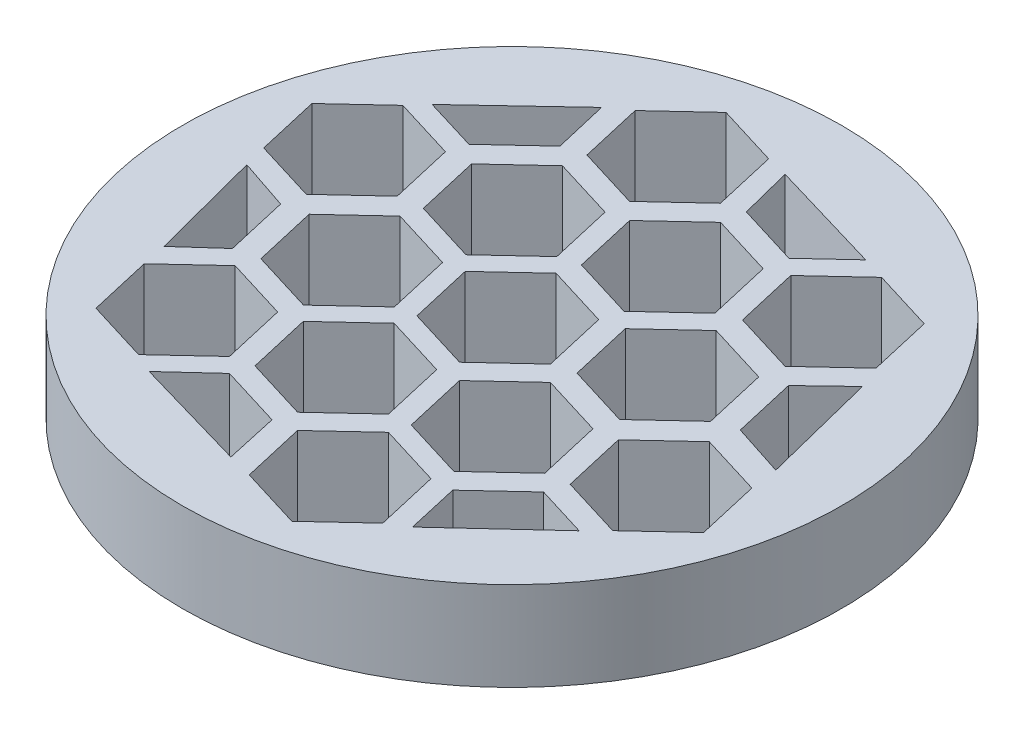
SolidWorks part; units mm, degrees
ref_plane "Ebene vorne" through (0, 0, 0) normal (0, 0, 1) x (1, 0, 0)
ref_plane "Ebene oben" through (0, 0, 0) normal (0, 1, 0) x (1, 0, 0)
ref_plane "Ebene rechts" through (0, 0, 0) normal (1, 0, 0) x (0, 0, -1)
sketch "Skizze1" plane through (0, 0, 0) normal (0, 1, 0) x (1, 0, 0)
  line L0 (3.1154, 1.2037) -> (3.4388, 2.6104)
  line L1 (1.0565, -0.9834) -> (1.3799, 0.4233)
  line L2 (1.3799, 0.4233) -> (0.3234, 1.4067)
  line L3 (0.3234, 1.4067) -> (-1.0565, 0.9834)
  line L4 (-1.0565, 0.9834) -> (-1.3799, -0.4233)
  line L5 (-1.3799, -0.4233) -> (-0.3234, -1.4067)
  line L6 (-0.3234, -1.4067) -> (1.0565, -0.9834)
  line L7 (3.4388, 2.6104) -> (2.3823, 3.5938)
  line L8 (2.3823, 3.5938) -> (1.0024, 3.1705)
  line L9 (1.0024, 3.1705) -> (0.679, 1.7638)
  line L10 (0.679, 1.7638) -> (1.7355, 0.7804)
  line L11 (1.7355, 0.7804) -> (3.1154, 1.2037)
  line L12 (3.9678, -1.6662) -> (4.2912, -0.2595)
  line L13 (4.2912, -0.2595) -> (3.2347, 0.7239)
  line L14 (3.2347, 0.7239) -> (1.8548, 0.3007)
  line L15 (1.8548, 0.3007) -> (1.5314, -1.106)
  line L16 (1.5314, -1.106) -> (2.5879, -2.0894)
  line L17 (2.5879, -2.0894) -> (3.9678, -1.6662)
  line L18 (1.9136, -3.8196) -> (2.237, -2.413)
  line L19 (2.237, -2.413) -> (1.1804, -1.4296)
  line L20 (1.1804, -1.4296) -> (-0.1995, -1.8528)
  line L21 (-0.1995, -1.8528) -> (-0.5229, -3.2595)
  line L22 (-0.5229, -3.2595) -> (0.5337, -4.2429)
  line L23 (0.5337, -4.2429) -> (1.9136, -3.8196)
  line L24 (-0.9621, -3.1449) -> (-0.6387, -1.7382)
  line L25 (-0.6387, -1.7382) -> (-1.6952, -0.7548)
  line L26 (-1.6952, -0.7548) -> (-3.0751, -1.1781)
  line L27 (-3.0751, -1.1781) -> (-3.3985, -2.5847)
  line L28 (-3.3985, -2.5847) -> (-2.342, -3.5682)
  line L29 (-2.342, -3.5682) -> (-0.9621, -3.1449)
  line L30 (-1.8069, -0.3421) -> (-1.4835, 1.0646)
  line L31 (-1.4835, 1.0646) -> (-2.54, 2.048)
  line L32 (-2.54, 2.048) -> (-3.9199, 1.6247)
  line L33 (-3.9199, 1.6247) -> (-4.2433, 0.218)
  line L34 (-4.2433, 0.218) -> (-3.1868, -0.7654)
  line L35 (-3.1868, -0.7654) -> (-1.8069, -0.3421)
  line L36 (0.2105, 1.8075) -> (0.5339, 3.2142)
  line L37 (0.5339, 3.2142) -> (-0.5227, 4.1976)
  line L38 (-0.5227, 4.1976) -> (-1.9026, 3.7743)
  line L39 (-1.9026, 3.7743) -> (-2.226, 2.3676)
  line L40 (-2.226, 2.3676) -> (-1.1694, 1.3842)
  line L41 (-1.1694, 1.3842) -> (0.2105, 1.8075)
  line L42 (6.052, 0.5724) -> (6.3754, 1.9791)
  line L43 (6.3754, 1.9791) -> (5.3189, 2.9625)
  line L44 (5.3189, 2.9625) -> (3.9389, 2.5392)
  line L45 (3.9389, 2.5392) -> (3.6155, 1.1325)
  line L46 (3.6155, 1.1325) -> (4.6721, 0.1491)
  line L47 (4.6721, 0.1491) -> (6.052, 0.5724)
  line L48 (4.7915, -4.5582) -> (5.1149, -3.1515)
  line L49 (5.1149, -3.1515) -> (4.0584, -2.1681)
  line L50 (4.0584, -2.1681) -> (2.6785, -2.5913)
  line L51 (2.6785, -2.5913) -> (2.3551, -3.998)
  line L52 (2.3551, -3.998) -> (3.4116, -4.9814)
  line L53 (3.4116, -4.9814) -> (4.7915, -4.5582)
  line L54 (-0.1625, -6.0189) -> (0.1609, -4.6123)
  line L55 (0.1609, -4.6123) -> (-0.8956, -3.6288)
  line L56 (-0.8956, -3.6288) -> (-2.2755, -4.0521)
  line L57 (-2.2755, -4.0521) -> (-2.5989, -5.4588)
  line L58 (-2.5989, -5.4588) -> (-1.5424, -6.4422)
  line L59 (-1.5424, -6.4422) -> (-0.1625, -6.0189)
  line L60 (-3.9289, -2.5273) -> (-3.6055, -1.1206)
  line L61 (-3.6055, -1.1206) -> (-4.662, -0.1372)
  line L62 (-4.662, -0.1372) -> (-6.0419, -0.5605)
  line L63 (-6.0419, -0.5605) -> (-6.3653, -1.9672)
  line L64 (-6.3653, -1.9672) -> (-5.3088, -2.9506)
  line L65 (-5.3088, -2.9506) -> (-3.9289, -2.5273)
  line L66 (-2.6953, 2.4726) -> (-2.3719, 3.8793)
  line L67 (-2.3719, 3.8793) -> (-3.4285, 4.8627)
  line L68 (-3.4285, 4.8627) -> (-4.8084, 4.4394)
  line L69 (-4.8084, 4.4394) -> (-5.1318, 3.0327)
  line L70 (-5.1318, 3.0327) -> (-4.0752, 2.0493)
  line L71 (-4.0752, 2.0493) -> (-2.6953, 2.4726)
  line L72 (2.2673, 3.9927) -> (2.5907, 5.3994)
  line L73 (2.5907, 5.3994) -> (1.5342, 6.3828)
  line L74 (1.5342, 6.3828) -> (0.1543, 5.9596)
  line L75 (0.1543, 5.9596) -> (-0.1691, 4.5529)
  line L76 (-0.1691, 4.5529) -> (0.8874, 3.5695)
  line L77 (0.8874, 3.5695) -> (2.2673, 3.9927)
  line L80 (4.9443, 3.3426) -> (3.0002, 5.1403)
  line L81 (3.0002, 5.1403) -> (2.734, 3.9707)
  line L82 (2.734, 3.9707) -> (3.7905, 2.9873)
  line L83 (3.7905, 2.9873) -> (4.9443, 3.3426)
  line L85 (5.3189, -2.6446) -> (5.9726, -0.044)
  line L86 (5.9726, -0.044) -> (4.7938, -0.4264)
  line L87 (4.7938, -0.4264) -> (4.4704, -1.8331)
  line L88 (4.4704, -1.8331) -> (5.3189, -2.6446)
  line L90 (0.3234, -5.9024) -> (2.8926, -5.1427)
  line L91 (2.8926, -5.1427) -> (2.0003, -4.3124)
  line L92 (2.0003, -4.3124) -> (0.6203, -4.7356)
  line L93 (0.6203, -4.7356) -> (0.3234, -5.9024)
  line L96 (-3.0374, -5.1427) -> (-2.752, -3.9198)
  line L97 (-2.752, -3.9198) -> (-3.8085, -2.9364)
  line L98 (-3.8085, -2.9364) -> (-4.9977, -3.2977)
  line L101 (-4.9977, -3.2977) -> (-3.0374, -5.1427)
  line L102 (-4.7616, 0.3399) -> (-4.4382, 1.7466)
  line L103 (-4.4382, 1.7466) -> (-5.246, 2.4726)
  line L106 (-5.246, 2.4726) -> (-5.9047, -0.044)
  line L107 (-5.9047, -0.044) -> (-4.7616, 0.3399)
  line L108 (-0.6627, 4.6321) -> (-0.401, 5.8179)
  line L111 (-0.401, 5.8179) -> (-2.9819, 5.0719)
  line L112 (-2.9819, 5.0719) -> (-2.0426, 4.2088)
  line L113 (-2.0426, 4.2088) -> (-0.6627, 4.6321)
  circle A1 centre (0, 0) radius 1.25 construction
  circle A2 centre (0, 0) radius 7.4
extrude "Aufsatz-Linear austragen2" add sketch "Skizze1" along normal blind 2 contours A2
sketch "Skizze3" plane through (0, 0, 0) normal (0, -1, 0) x (1, 0, 0)
  line L0 (3.1104, 1.2923) -> (3.4338, 2.699)
  line L1 (1.0515, -0.8948) -> (1.3749, 0.5119)
  line L2 (1.3749, 0.5119) -> (0.3184, 1.4953)
  line L3 (0.3184, 1.4953) -> (-1.0616, 1.072)
  line L4 (-1.0616, 1.072) -> (-1.385, -0.3347)
  line L5 (-1.385, -0.3347) -> (-0.3284, -1.3181)
  line L6 (-0.3284, -1.3181) -> (1.0515, -0.8948)
  line L7 (3.4338, 2.699) -> (2.3772, 3.6824)
  line L8 (2.3772, 3.6824) -> (0.9973, 3.2591)
  line L9 (0.9973, 3.2591) -> (0.6739, 1.8524)
  line L10 (0.6739, 1.8524) -> (1.7304, 0.869)
  line L11 (1.7304, 0.869) -> (3.1104, 1.2923)
  line L12 (3.9628, -1.5776) -> (4.2862, -0.1709)
  line L13 (4.2862, -0.1709) -> (3.2297, 0.8125)
  line L14 (3.2297, 0.8125) -> (1.8497, 0.3893)
  line L15 (1.8497, 0.3893) -> (1.5263, -1.0174)
  line L16 (1.5263, -1.0174) -> (2.5829, -2.0008)
  line L17 (2.5829, -2.0008) -> (3.9628, -1.5776)
  line L18 (1.9085, -3.7311) -> (2.2319, -2.3244)
  line L19 (2.2319, -2.3244) -> (1.1754, -1.341)
  line L20 (1.1754, -1.341) -> (-0.2045, -1.7642)
  line L21 (-0.2045, -1.7642) -> (-0.5279, -3.1709)
  line L22 (-0.5279, -3.1709) -> (0.5286, -4.1543)
  line L23 (0.5286, -4.1543) -> (1.9085, -3.7311)
  line L24 (-0.9671, -3.0563) -> (-0.6437, -1.6496)
  line L25 (-0.6437, -1.6496) -> (-1.7002, -0.6662)
  line L26 (-1.7002, -0.6662) -> (-3.0802, -1.0895)
  line L27 (-3.0802, -1.0895) -> (-3.4036, -2.4962)
  line L28 (-3.4036, -2.4962) -> (-2.347, -3.4796)
  line L29 (-2.347, -3.4796) -> (-0.9671, -3.0563)
  line L30 (-1.8119, -0.2535) -> (-1.4885, 1.1532)
  line L31 (-1.4885, 1.1532) -> (-2.5451, 2.1366)
  line L32 (-2.5451, 2.1366) -> (-3.925, 1.7133)
  line L33 (-3.925, 1.7133) -> (-4.2484, 0.3066)
  line L34 (-4.2484, 0.3066) -> (-3.1918, -0.6768)
  line L35 (-3.1918, -0.6768) -> (-1.8119, -0.2535)
  line L36 (0.2054, 1.8961) -> (0.5288, 3.3028)
  line L37 (0.5288, 3.3028) -> (-0.5277, 4.2862)
  line L38 (-0.5277, 4.2862) -> (-1.9076, 3.8629)
  line L39 (-1.9076, 3.8629) -> (-2.231, 2.4562)
  line L40 (-2.231, 2.4562) -> (-1.1745, 1.4728)
  line L41 (-1.1745, 1.4728) -> (0.2054, 1.8961)
  line L42 (6.0469, 0.661) -> (6.3703, 2.0676)
  line L43 (6.3703, 2.0676) -> (5.3138, 3.0511)
  line L44 (5.3138, 3.0511) -> (3.9339, 2.6278)
  line L45 (3.9339, 2.6278) -> (3.6105, 1.2211)
  line L46 (3.6105, 1.2211) -> (4.667, 0.2377)
  line L47 (4.667, 0.2377) -> (6.0469, 0.661)
  line L48 (4.7865, -4.4696) -> (5.1099, -3.0629)
  line L49 (5.1099, -3.0629) -> (4.0533, -2.0795)
  line L50 (4.0533, -2.0795) -> (2.6734, -2.5028)
  line L51 (2.6734, -2.5028) -> (2.35, -3.9094)
  line L52 (2.35, -3.9094) -> (3.4065, -4.8928)
  line L53 (3.4065, -4.8928) -> (4.7865, -4.4696)
  line L54 (-0.1675, -5.9304) -> (0.1559, -4.5237)
  line L55 (0.1559, -4.5237) -> (-0.9007, -3.5403)
  line L56 (-0.9007, -3.5403) -> (-2.2806, -3.9635)
  line L57 (-2.2806, -3.9635) -> (-2.604, -5.3702)
  line L58 (-2.604, -5.3702) -> (-1.5474, -6.3536)
  line L59 (-1.5474, -6.3536) -> (-0.1675, -5.9304)
  line L60 (-3.9339, -2.4387) -> (-3.6105, -1.0321)
  line L61 (-3.6105, -1.0321) -> (-4.667, -0.0486)
  line L62 (-4.667, -0.0486) -> (-6.0469, -0.4719)
  line L63 (-6.0469, -0.4719) -> (-6.3703, -1.8786)
  line L64 (-6.3703, -1.8786) -> (-5.3138, -2.862)
  line L65 (-5.3138, -2.862) -> (-3.9339, -2.4387)
  line L66 (-2.7004, 2.5612) -> (-2.377, 3.9678)
  line L67 (-2.377, 3.9678) -> (-3.4335, 4.9513)
  line L68 (-3.4335, 4.9513) -> (-4.8134, 4.528)
  line L69 (-4.8134, 4.528) -> (-5.1368, 3.1213)
  line L70 (-5.1368, 3.1213) -> (-4.0803, 2.1379)
  line L71 (-4.0803, 2.1379) -> (-2.7004, 2.5612)
  line L72 (2.2623, 4.0813) -> (2.5857, 5.488)
  line L73 (2.5857, 5.488) -> (1.5292, 6.4714)
  line L74 (1.5292, 6.4714) -> (0.1493, 6.0481)
  line L75 (0.1493, 6.0481) -> (-0.1741, 4.6415)
  line L76 (-0.1741, 4.6415) -> (0.8824, 3.6581)
  line L77 (0.8824, 3.6581) -> (2.2623, 4.0813)
  line L78 (4.9393, 3.4311) -> (2.9952, 5.2289)
  line L79 (2.9952, 5.2289) -> (2.7289, 4.0593)
  line L80 (2.7289, 4.0593) -> (3.7855, 3.0759)
  line L81 (3.7855, 3.0759) -> (4.9393, 3.4311)
  line L82 (5.3138, -2.556) -> (5.9675, 0.0446)
  line L83 (5.9675, 0.0446) -> (4.7887, -0.3379)
  line L84 (4.7887, -0.3379) -> (4.4653, -1.7445)
  line L85 (4.4653, -1.7445) -> (5.3138, -2.556)
  line L86 (0.3184, -5.8138) -> (2.8876, -5.0541)
  line L87 (2.8876, -5.0541) -> (1.9952, -4.2238)
  line L88 (1.9952, -4.2238) -> (0.6153, -4.647)
  line L89 (0.6153, -4.647) -> (0.3184, -5.8138)
  line L90 (-3.0425, -5.0541) -> (-2.7571, -3.8312)
  line L91 (-2.7571, -3.8312) -> (-3.8136, -2.8478)
  line L92 (-3.8136, -2.8478) -> (-5.0027, -3.2091)
  line L93 (-5.0027, -3.2091) -> (-3.0425, -5.0541)
  line L94 (-4.7667, 0.4285) -> (-4.4433, 1.8351)
  line L95 (-4.4433, 1.8351) -> (-5.2511, 2.5612)
  line L96 (-5.2511, 2.5612) -> (-5.9097, 0.0446)
  line L97 (-5.9097, 0.0446) -> (-4.7667, 0.4285)
  line L98 (-0.6678, 4.7207) -> (-0.406, 5.9065)
  line L99 (-0.406, 5.9065) -> (-2.9869, 5.1605)
  line L100 (-2.9869, 5.1605) -> (-2.0477, 4.2974)
  line L101 (-2.0477, 4.2974) -> (-0.6678, 4.7207)
extrude "Schnitt-Linear austragen2" cut sketch "Skizze3" against normal blind 2
